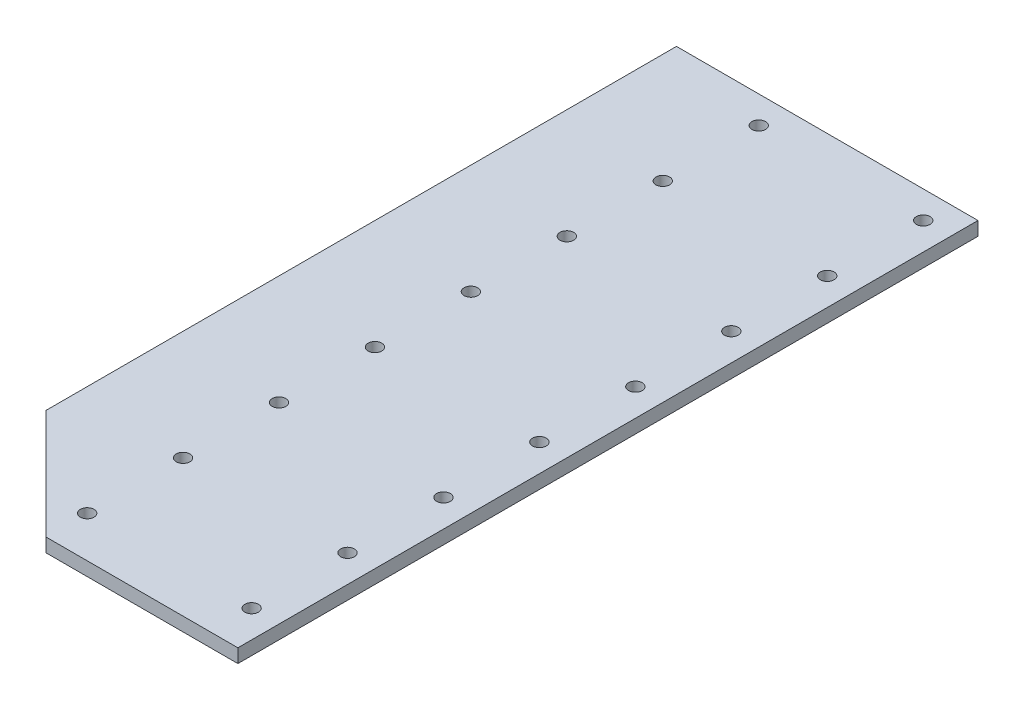
SolidWorks part; units mm, degrees
ref_plane "Front Plane" through (0, 0, 0) normal (0, 0, 1) x (1, 0, 0)
ref_plane "Top Plane" through (0, 0, 0) normal (0, 1, 0) x (1, 0, 0)
ref_plane "Right Plane" through (0, 0, 0) normal (1, 0, 0) x (0, 0, -1)
sketch "Sketch1" plane through (0, 0, 0) normal (0, 1, 0) x (1, 0, 0)
  line L0 (40, 301.9965) -> (40, -67.5183) construction
  line L2 (0, 0) -> (0, 230)
  line L3 (0, 230) -> (110, 230)
  line L4 (110, -35) -> (110, 230)
  line L7 (110, -40) -> (110, -35)
  line L8 (0, 0) -> (40, -40)
  line L9 (40, -40) -> (110, -40)
  circle A0 centre (40, 220) radius 2.5
  circle A1 centre (100, 220) radius 2.5
  circle A2 centre (40, 185) radius 2.5
  circle A3 centre (100, 185) radius 2.5
  circle A4 centre (40, 150) radius 2.5
  circle A5 centre (100, 150) radius 2.5
  circle A6 centre (40, 115) radius 2.5
  circle A7 centre (100, 115) radius 2.5
  circle A8 centre (40, 80) radius 2.5
  circle A9 centre (100, 80) radius 2.5
  circle A10 centre (40, 45) radius 2.5
  circle A11 centre (100, 45) radius 2.5
  circle A12 centre (40, 10) radius 2.5
  circle A13 centre (100, 10) radius 2.5
  circle A14 centre (40, -25) radius 2.5
  circle A15 centre (100, -25) radius 2.5
  dimension "D2" = 5
  dimension "D1" = 60
  dimension "D3" = 10
  dimension "D4" = 40
  dimension "D5" = 10
  dimension "D7" = 230
  dimension "D6" = 8
extrude "Boss-Extrude1" add sketch "Sketch1" along normal blind 5
